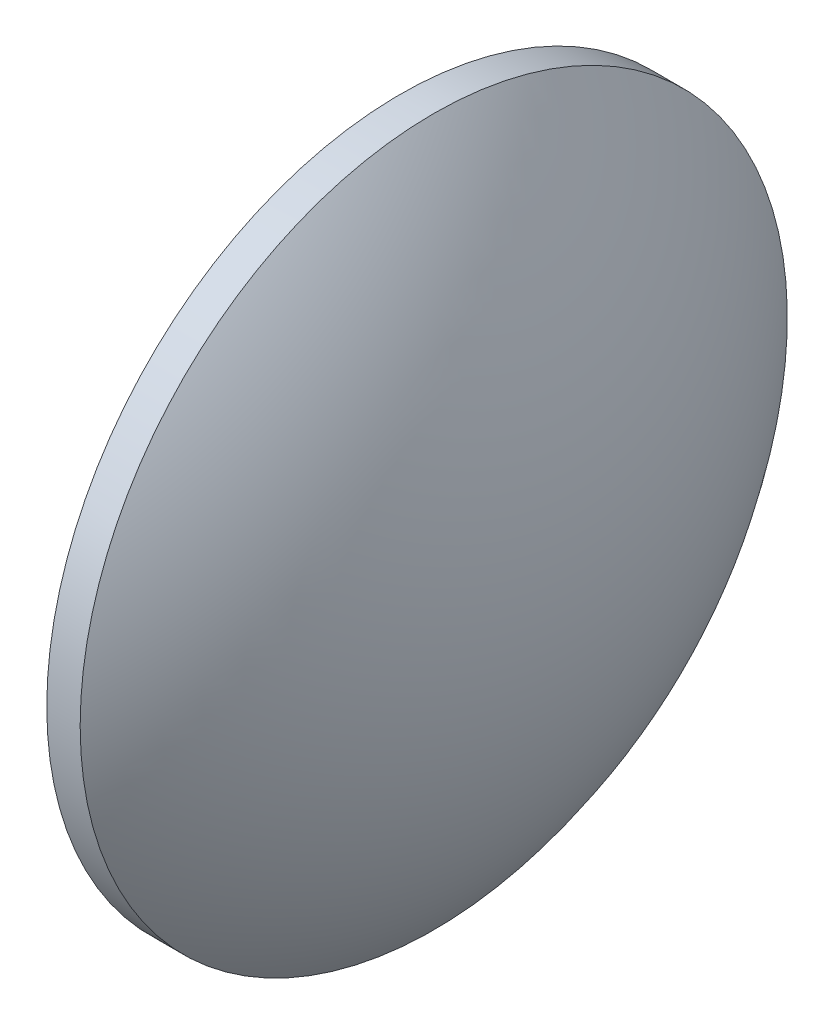
SolidWorks part; units mm, degrees
ref_plane "前视基准面" through (0, 0, 0) normal (0, 0, 1) x (1, 0, 0)
ref_plane "上视基准面" through (0, 0, 0) normal (0, 1, 0) x (1, 0, 0)
ref_plane "右视基准面" through (0, 0, 0) normal (1, 0, 0) x (0, 0, -1)
sketch "草图1" plane through (0, 0, 0) normal (0, 0, 1) x (1, 0, 0)
  line L0 (374.0107, 55.9227) -> (392.8067, 55.9227) construction
  line L1 (379.5886, 55.9227) -> (379.5886, 73.9227)
  line L2 (379.5886, 73.9227) -> (381.2886, 73.9227)
  line L3 (387.5886, 55.9227) -> (379.5886, 55.9227)
  arc A0 (387.5886, 55.9227) -> (381.2886, 73.9227) centre (358.7244, 55.9227) ccw
revolve "旋转1" add sketch "草图1" angle 360 about L0
